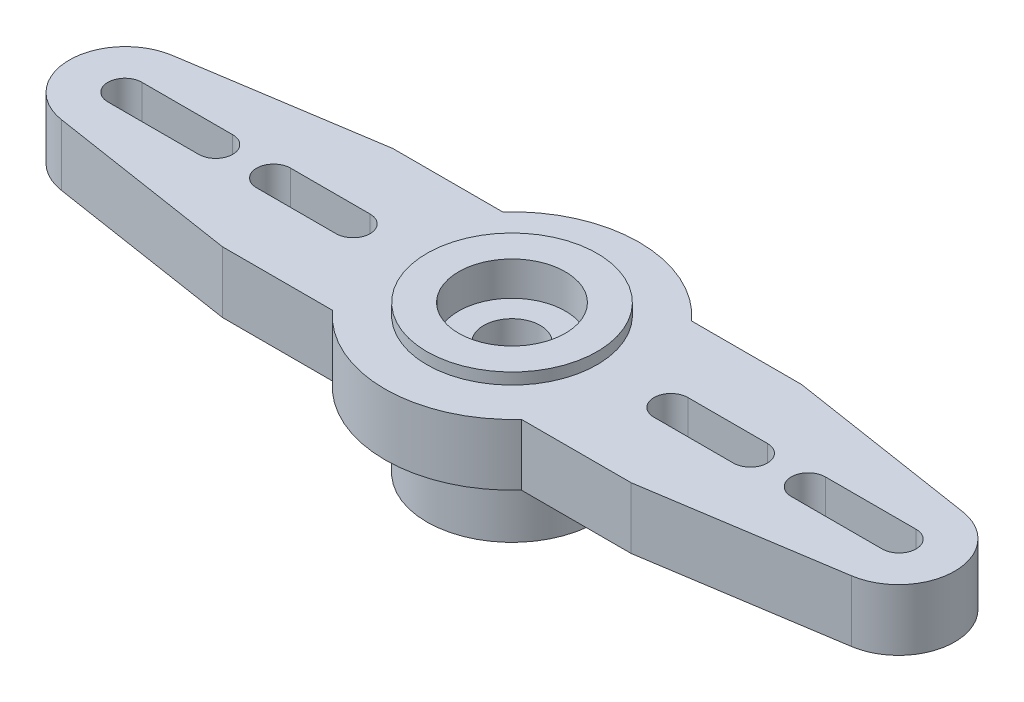
SolidWorks part; units mm, degrees
material "PVC 0.007 Plasticized"
ref_plane "Front Plane" through (0, 0, 0) normal (0, 0, 1) x (1, 0, 0)
ref_plane "Top Plane" through (0, 0, 0) normal (0, 1, 0) x (1, 0, 0)
ref_plane "Right Plane" through (0, 0, 0) normal (1, 0, 0) x (0, 0, -1)
sketch "Sketch2" plane through (0, 0, 0) normal (0, 1, 0) x (1, 0, 0)
  circle A0 centre (0, 0) radius 3.75
  dimension "D1" = 7.5
extrude "Boss-Extrude1" add sketch "Sketch2" along normal blind 6.5
sketch "Sketch3" plane through (0, 6.5, 0) normal (0, 1, 0) x (1, 0, 0)
  circle A0 centre (0, 0) radius 1.25
  dimension "D1" = 2.5
extrude "Cut-Extrude1" cut sketch "Sketch3" against normal through all both and the other way through all
sketch "Sketch4" plane through (0, 6.5, 0) normal (0, 1, 0) x (1, 0, 0)
  circle A0 centre (0, 0) radius 2.35
  dimension "D1" = 4.7
extrude "Cut-Extrude2" cut sketch "Sketch4" against normal blind 1.5 and the other way through all
sketch "Sketch7" plane through (0, 0, 0) normal (0, -1, 0) x (1, 0, 0)
  circle A0 centre (0, 0) radius 2.35 construction
  circle A1 centre (0, 0) radius 2.35
extrude "Cut-Extrude5" cut sketch "Sketch7" against normal blind 3.4
ref_plane "Plane1" through (0, 6, 0) normal (0, 1, 0) x (1, 0, 0)
sketch "Sketch8" plane through (0, 6, 0) normal (0, 1, 0) x (1, 0, 0)
  line L0 (0, 0) -> (19.5, 0) construction
  line L3 (0, -9.55) -> (0, 9.55) construction
  line L4 (7, 0.75) -> (10.5, 0.75)
  line L5 (7, -0.75) -> (10.5, -0.75)
  line L6 (13.05, 0.75) -> (17.05, 0.75)
  line L7 (13.05, -0.75) -> (17.05, -0.75)
  line L8 (-9, 3.75) -> (9, 3.75)
  line L9 (9, 3.75) -> (17.4045, 2.4457)
  line L14 (9, -3.75) -> (17.4045, -2.4457)
  line L15 (-9, -3.75) -> (9, -3.75)
  line L18 (-13.05, -0.75) -> (-17.05, -0.75)
  line L19 (-13.05, 0.75) -> (-17.05, 0.75)
  line L20 (-7, -0.75) -> (-10.5, -0.75)
  line L21 (-7, 0.75) -> (-10.5, 0.75)
  line L24 (-9, -3.75) -> (-17.4045, -2.4457)
  line L25 (-9, 3.75) -> (-17.4045, 2.4457)
  circle A0 centre (0, 0) radius 3.75 construction
  arc A2 (17.4045, -2.4457) -> (17.4045, 2.4457) centre (17.025, 0) ccw
  arc A3 (7, 0.75) -> (7, -0.75) centre (7, 0) ccw
  arc A4 (10.5, -0.75) -> (10.5, 0.75) centre (10.5, 0) ccw
  arc A5 (13.05, 0.75) -> (13.05, -0.75) centre (13.05, 0) ccw
  arc A6 (17.05, -0.75) -> (17.05, 0.75) centre (17.05, 0) ccw
  circle A12 centre (0, 0) radius 5.6
  arc A15 (-17.4045, -2.4457) -> (-17.4045, 2.4457) centre (-17.025, 0) cw
  arc A16 (-13.05, 0.75) -> (-13.05, -0.75) centre (-13.05, 0) cw
  arc A17 (-17.05, -0.75) -> (-17.05, 0.75) centre (-17.05, 0) cw
  arc A18 (-7, 0.75) -> (-7, -0.75) centre (-7, 0) cw
  arc A19 (-10.5, -0.75) -> (-10.5, 0.75) centre (-10.5, 0) cw
  circle A20 centre (0, 0) radius 3.75
  point P18 (0, 0)
  point P26 (0, -3.75)
  point P27 (0, 3.75)
  dimension "D1" = 19.5
  dimension "D2" = 4.95
  dimension "D5" = 2.45
  dimension "D7" = 11.2
  dimension "D8" = 18
  dimension "D10" = 0.75
  dimension "D13" = 0.75
  dimension "D3" = 7
  dimension "D4" = 3.5
  dimension "D6" = 4
extrude "Boss-Extrude4" add sketch "Sketch8" against normal blind 2.7
